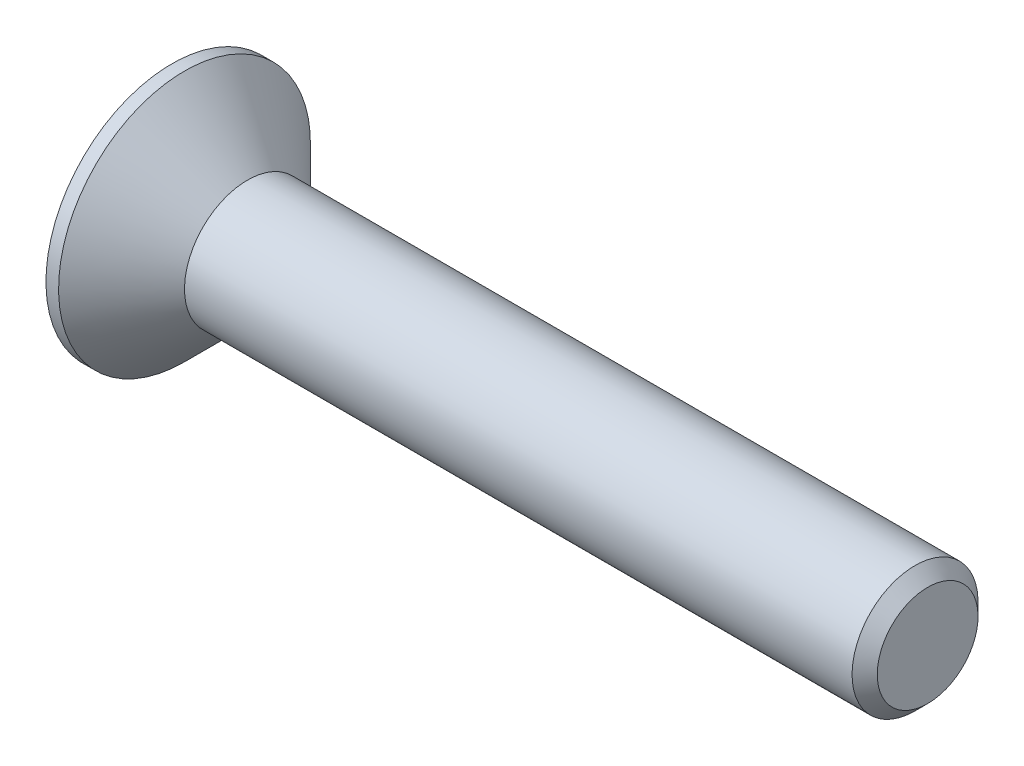
SolidWorks part; units mm, degrees
ref_plane "Front Plane" through (0, 0, 0) normal (0, 0, 1) x (1, 0, 0)
ref_plane "Top Plane" through (0, 0, 0) normal (0, 1, 0) x (1, 0, 0)
ref_plane "Right Plane" through (0, 0, 0) normal (1, 0, 0) x (0, 0, -1)
sketch "Sketch1" plane through (0, 0, 0) normal (0, 0, 1) x (1, 0, 0)
  line L0 (0, 1) -> (-1, 2)
  line L1 (-1, 2) -> (-1.2, 2)
  line L2 (-1.2, 2) -> (-1.2, 0)
  line L3 (-1.2, 0) -> (10.8, 0)
  line L4 (10.8, 0) -> (10.8, 1)
  line L5 (10.8, 1) -> (0, 1)
  point P2 (0, 0)
  dimension "D1" = 1
  dimension "D2" = 12
  dimension "D3" = 45
  dimension "D4" = 2
  dimension "D5" = 1.2
revolve "Revolve1" add sketch "Sketch1" angle 360 about L3
chamfer "Chamfer1" distance 0.2 angle 45 1 edges at (10.8, -1, 0)
sketch "Sketch2" plane through (-1.2, 0, 0) normal (-1, 0, 0) x (0, 0, 1)
  line L1 (-0.7506, 0) -> (-0.3753, -0.65)
  line L2 (-0.3753, -0.65) -> (0.3753, -0.65)
  line L3 (0.3753, -0.65) -> (0.7506, 0)
  line L4 (0.7506, 0) -> (0.3753, 0.65)
  line L5 (0.3753, 0.65) -> (-0.3753, 0.65)
  line L6 (-0.3753, 0.65) -> (-0.7506, 0)
  circle A0 centre (0, 0) radius 0.65 construction
  point P1 (0, 0)
  dimension "D1" = 1.3
extrude "Cut-Extrude1" cut sketch "Sketch2" against normal blind 0.75
